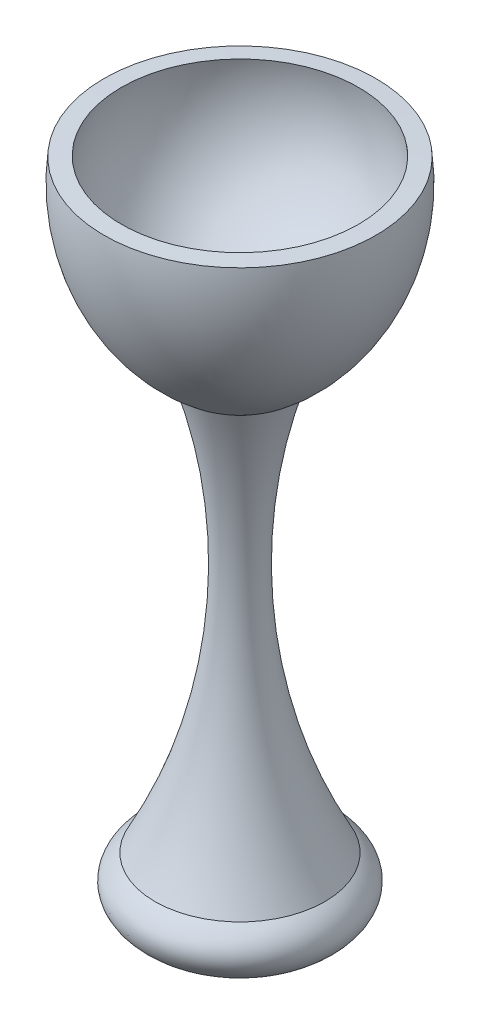
SolidWorks part; units mm, degrees
ref_plane "Front Plane" through (0, 0, 0) normal (0, 0, 1) x (1, 0, 0)
ref_plane "Top Plane" through (0, 0, 0) normal (0, 1, 0) x (1, 0, 0)
ref_plane "Right Plane" through (0, 0, 0) normal (1, 0, 0) x (0, 0, -1)
sketch "Sketch1" plane through (0, 0, 0) normal (0, 0, 1) x (1, 0, 0)
  line L0 (0, 50.8) -> (0, -50.8) construction
  line L1 (-42.291, -254) -> (42.291, -254) construction
  line L2 (0, -50.8) -> (0, -273.05)
  line L3 (57.1147, 9.3859) -> (49.8516, 9.7704)
  line L4 (19.8651, -70.6651) -> (0, -50.8) construction
  arc A0 (49.8516, 9.7704) -> (0, 50.8) centre (0, 0) ccw construction
  arc A1 (0, 50.8) -> (0, -50.8) centre (0, 0) ccw construction
  arc A3 (35.707, -243.7922) -> (19.8651, -70.6651) centre (232.8546, -138.464) cw
  arc A4 (0, -50.8) -> (32.7793, -38.8093) centre (0, 0) ccw
  arc A5 (19.8651, -70.6651) -> (57.1147, 9.3859) centre (-27.0031, -0.1642) ccw
  arc A6 (19.8651, -70.6651) -> (32.7793, -38.8093) centre (232.8546, -138.464) cw construction
  arc A7 (32.7793, -38.8093) -> (49.8516, 9.7704) centre (0, 0) ccw
  ellipse E0 centre (0, -254) end of major axis (-42.291, -254) minor radius 19.05 (0, -273.05) -> (35.707, -243.7922) ccw
  ellipse E1 centre (0, -254) end of major axis (-42.291, -254) minor radius 19.05 (35.707, -243.7922) -> (0, -234.95) ccw construction
  ellipse E2 centre (0, -254) end of major axis (-42.291, -254) minor radius 19.05 (0, -234.95) -> (-42.291, -254) ccw construction
  ellipse E3 centre (0, -254) end of major axis (-42.291, -254) minor radius 19.05 (-42.291, -254) -> (0, -273.05) ccw construction
  dimension "D1" = 101.6
  dimension "D4" = 223.52
  dimension "D5" = 84.6582
  dimension "D2" = 84.582
  dimension "D3" = 38.1
  dimension "D6" = 45
  dimension "D7" = 254
revolve "Revolve1" add sketch "Sketch1" angle 360 about L2
